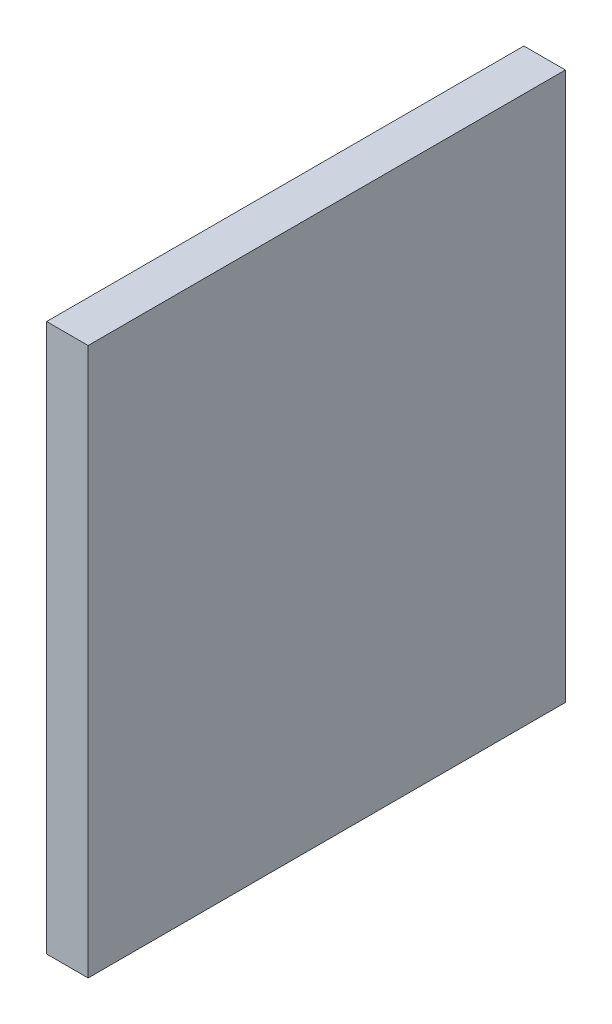
SolidWorks part; units mm, degrees
material "POLYURETHANE (11671)"
ref_plane "Front Plane" through (0, 0, 0) normal (0, 0, 1) x (1, 0, 0)
ref_plane "Top Plane" through (0, 0, 0) normal (0, 1, 0) x (1, 0, 0)
ref_plane "Right Plane" through (0, 0, 0) normal (1, 0, 0) x (0, 0, -1)
sketch "Sketch1" plane through (0, 0, 0) normal (1, 0, 0) x (0, 0, -1)
  line L1 (-18.2563, -20.955) -> (18.2562, -20.955)
  line L2 (-18.2563, -20.955) -> (-18.2563, 20.955)
  line L3 (-18.2563, 20.955) -> (18.2562, 20.955)
  line L4 (18.2562, -20.955) -> (18.2562, 20.955)
  line L5 (-18.2563, -20.955) -> (18.2562, 20.955) construction
  line L6 (-18.2563, 20.955) -> (18.2562, -20.955) construction
  point P0 (0, 0)
  dimension "D1" = 36.5125
  dimension "D2" = 41.91
extrude "Boss-Extrude1" add sketch "Sketch1" along normal blind 3.175
